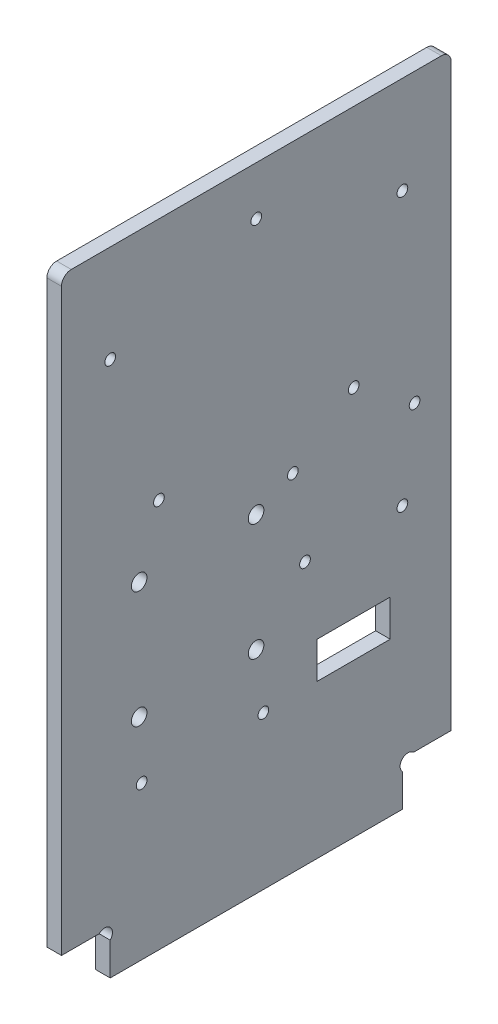
SolidWorks part; units mm, degrees
ref_plane "Plan de face" through (0, 0, 0) normal (0, 0, 1) x (1, 0, 0)
ref_plane "Plan de dessus" through (0, 0, 0) normal (0, 1, 0) x (1, 0, 0)
ref_plane "Plan de droite" through (0, 0, 0) normal (1, 0, 0) x (0, 0, -1)
sketch "Esquisse1" plane through (0, 0, 0) normal (1, 0, 0) x (0, 0, -1)
  line L8 (10, 6.7373) -> (10, 0)
  line L9 (70, 6.7373) -> (70, 0)
  line L10 (7.7373, 9) -> (0, 9)
  line L11 (10, 0) -> (70, 0)
  line L12 (72.2627, 9) -> (80, 9)
  line L13 (0, 9) -> (0, 130)
  line L14 (0, 130) -> (80, 130)
  line L15 (80, 130) -> (80, 9)
  arc A0 (10, 6.7373) -> (7.7373, 9) centre (8.8686, 7.8686) ccw
  arc A1 (70, 6.7373) -> (72.2627, 9) centre (71.1314, 7.8686) cw
  dimension "D7" = 1.1314
  dimension "D6" = 1.6
  dimension "D1" = 9
  dimension "D2" = 10
  dimension "D3" = 10
  dimension "D4" = 80
  dimension "D5" = 130
  dimension "D8" = 1.1314
  dimension "D9" = 1.1314
  dimension "D10" = 1.1314
extrude "Extrusion1" add sketch "Esquisse1" along normal blind 3
sketch "Esquisse2" plane through (3, 0, 0) normal (1, 0, 0) x (0, 0, -1)
  line L0 (0, 9) -> (7.7373, 9) construction
  line L1 (0, 130) -> (0, 9) construction
  line L2 (80, 9) -> (80, 130) construction
  line L3 (72.2627, 9) -> (80, 9) construction
  line L4 (80, 130) -> (0, 130) construction
  circle A0 centre (60, 80) radius 1.1
  circle A1 centre (10, 110) radius 1.1
  circle A2 centre (20, 80) radius 1.1
  circle A3 centre (70, 110) radius 1.1
  circle A4 centre (15.95, 67.45) radius 1.6
  circle A5 centre (15.95, 43.45) radius 1.6
  circle A6 centre (39.95, 43.45) radius 1.6
  circle A7 centre (39.95, 67.45) radius 1.6
  circle A8 centre (40, 120) radius 1.1
  circle A9 centre (70, 54) radius 1.1
  circle A10 centre (50, 54) radius 1.1
  dimension "D5" = 15.95
  dimension "D7" = 10
  dimension "D9" = 10
  dimension "D4" = 3.2
  dimension "D6" = 2.2
  dimension "D1" = 58.45
  dimension "D2" = 24
  dimension "D3" = 24
  dimension "D8" = 40
  dimension "D10" = 30
  dimension "D11" = 10
  dimension "D12" = 20
  dimension "D13" = 10
  dimension "D14" = 10
  dimension "D15" = 10
  dimension "D16" = 20
  dimension "D17" = 45
extrude "Enlèv. mat.-Extru.1" cut sketch "Esquisse2" against normal through all
sketch "Esquisse3" plane through (0, 0, 0) normal (-1, 0, 0) x (0, 0, 1)
  line L1 (-67.5, 39) -> (-52.5, 39)
  line L2 (-67.5, 39) -> (-67.5, 31.5)
  line L3 (-67.5, 31.5) -> (-52.5, 31.5)
  line L4 (-52.5, 39) -> (-52.5, 31.5)
  circle A0 centre (-70, 54) radius 1.1 construction
  circle A1 centre (-50, 54) radius 1.1 construction
  dimension "D4" = 2.5
  dimension "D1" = 15
  dimension "D2" = 7.5
  dimension "D3" = 15
  dimension "D5" = 2.5
extrude "Enlèv. mat.-Extru.2" cut sketch "Esquisse3" against normal through all
sketch "Esquisse4" plane through (3, 0, 0) normal (1, 0, 0) x (0, 0, -1)
  line L3 (0, 9) -> (7.7373, 9) construction
  line L4 (0, 130) -> (0, 9) construction
  line L5 (80, 9) -> (80, 130) construction
  circle A2 centre (75, 18) radius 1
  circle A3 centre (5, 18) radius 1
  dimension "D1" = 5
  dimension "D3" = 2
  dimension "D2" = 5
  dimension "D5" = 9
extrude "Enlèv. mat.-Extru.3" [suppressed] cut sketch "Esquisse4" against normal through all
fillet "Congé1" radius 2 2 edges at (1.5, 130, -80) (1.5, 130, 0)
sketch "Esquisse5" plane through (3, 0, 0) normal (1, 0, 0) x (0, 0, -1)
  line L0 (52.5, 31.5) -> (52.5, 39) construction
  line L1 (67.5, 39) -> (67.5, 31.5) construction
  circle A0 centre (16.45, 31.45) radius 1.1
  circle A1 centre (41.45, 31.45) radius 1.1
  circle A2 centre (47.5, 71) radius 1.1
  circle A3 centre (72.5, 71) radius 1.1
  circle A4 centre (15.95, 43.45) radius 1.6 construction
  circle A7 centre (50, 54) radius 1.1 construction
  dimension "D1" = 2.2
  dimension "D2" = 0.5
  dimension "D5" = 12
  dimension "D6" = 5
  dimension "D3" = 25
  dimension "D4" = 17
  dimension "D7" = 5
extrude "Enlèv. mat.-Extru.6" cut sketch "Esquisse5" against normal through all
